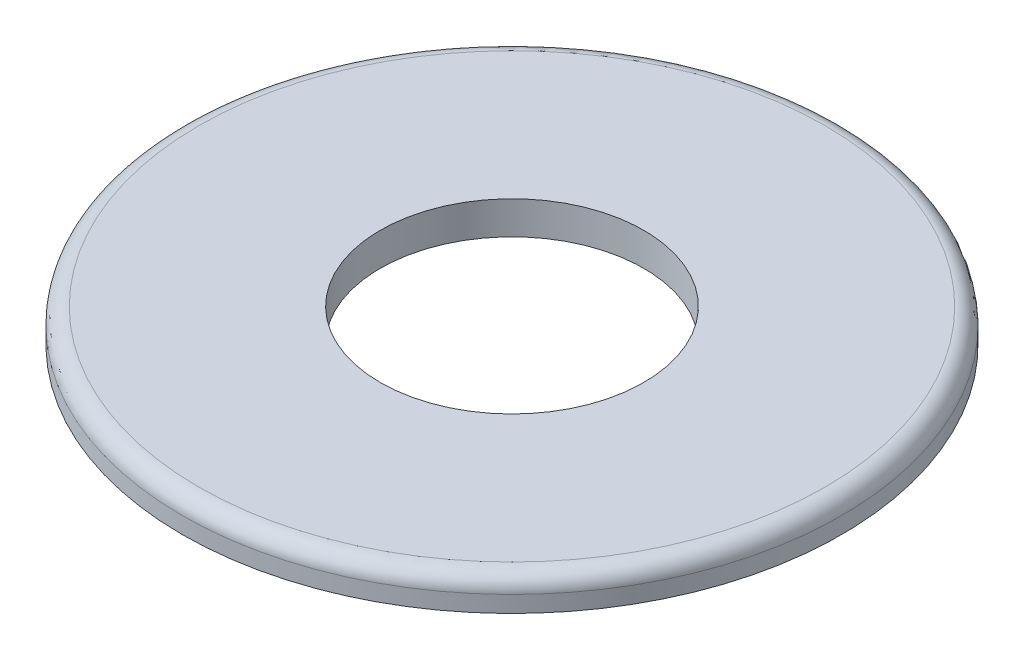
SolidWorks part; units mm, degrees
material "Green plastic appearance"
ref_plane "Front Plane" through (0, 0, 0) normal (0, 0, 1) x (1, 0, 0)
ref_plane "Top Plane" through (0, 0, 0) normal (0, 1, 0) x (1, 0, 0)
ref_plane "Right Plane" through (0, 0, 0) normal (1, 0, 0) x (0, 0, -1)
sketch "Sketch1" plane through (0, 0, 0) normal (0, 1, 0) x (1, 0, 0)
  circle A0 centre (0, 0) radius 10
  circle A1 centre (0, 0) radius 4
  dimension "D1" = 8
  dimension "D2" = 20
extrude "Boss-Extrude1" add sketch "Sketch1" along normal blind 1
fillet "Fillet1" radius 0.5 1 edges at (0, 1, 10)
